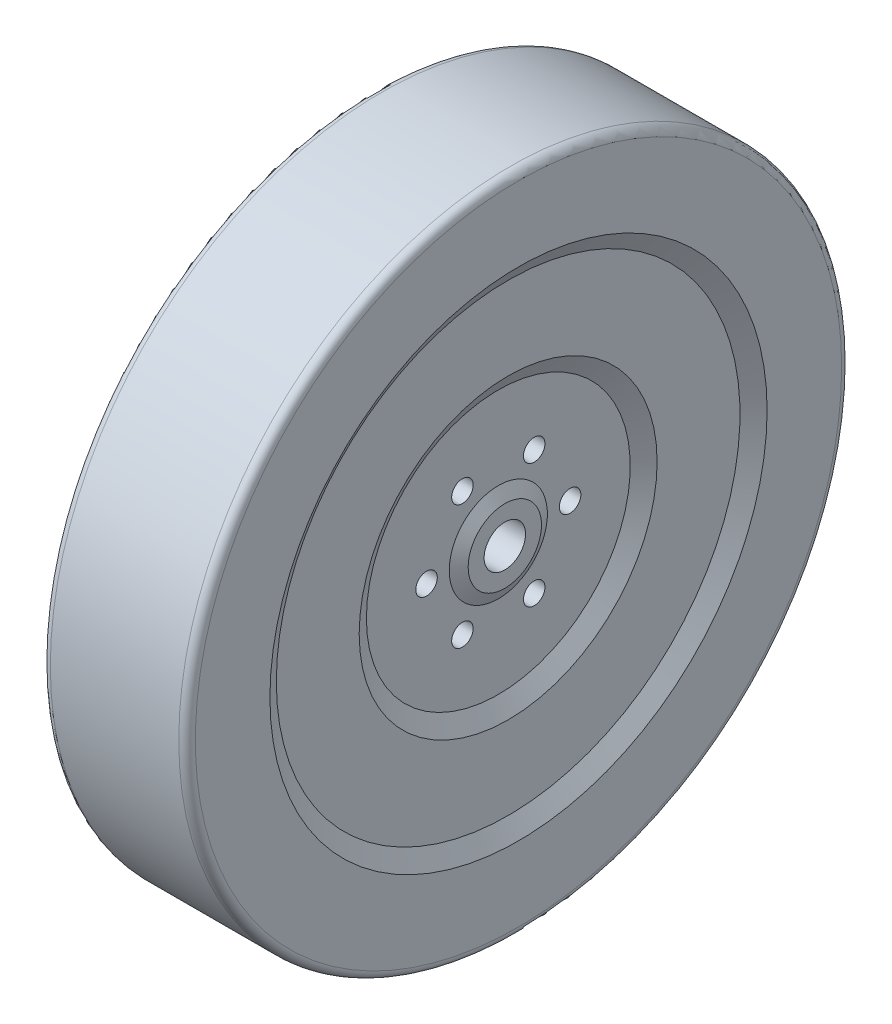
SolidWorks part; units mm, degrees
ref_plane "Front Plane" through (0, 0, 0) normal (0, 0, 1) x (1, 0, 0)
ref_plane "Top Plane" through (0, 0, 0) normal (0, 1, 0) x (1, 0, 0)
ref_plane "Right Plane" through (0, 0, 0) normal (1, 0, 0) x (0, 0, -1)
sketch "Sketch2" plane through (0, 0, 0) normal (0, 1, 0) x (1, 0, 0)
  line L1 (22.225, -101.6) -> (22.225, -76.2)
  line L2 (22.225, -76.2) -> (19.05, -71.0634)
  line L3 (19.05, -71.0634) -> (19.05, -45.6634)
  line L4 (19.05, -45.6634) -> (16.034, -40.4395)
  line L5 (16.034, -40.4395) -> (16.034, -15.0395)
  line L6 (16.034, -15.0395) -> (18.034, -11.2395)
  line L7 (18.034, -11.2395) -> (18.034, -6.35)
  line L10 (0, 0) -> (49.1946, 0) construction
  line L11 (0, 0) -> (0, -6.35) construction
  line L12 (-18.034, -6.35) -> (18.034, -6.35)
  line L13 (22.225, -101.6) -> (-22.225, -101.6)
  line L14 (0, -101.6) -> (0, -6.35) construction
  line L15 (-22.225, -101.6) -> (-22.225, -76.2)
  line L16 (-22.225, -76.2) -> (-19.05, -71.0634)
  line L17 (-19.05, -71.0634) -> (-19.05, -45.6634)
  line L18 (-19.05, -45.6634) -> (-16.034, -40.4395)
  line L19 (-16.034, -40.4395) -> (-16.034, -15.0395)
  line L20 (-16.034, -15.0395) -> (-18.034, -11.2395)
  line L21 (-18.034, -11.2395) -> (-18.034, -6.35)
  dimension "D1" = 18.034
  dimension "D2" = 22.225
  dimension "D3" = 25.4
  dimension "D4" = 25.4
  dimension "D5" = 25.4
  dimension "D6" = 4.8895
  dimension "D7" = 3.8
  dimension "D8" = 6.35
  dimension "D9" = 2
  dimension "D10" = 101.6
  dimension "D11" = 19.05
  dimension "D12" = 30
revolve "Revolve1" add sketch "Sketch2" angle 360 about L10
sketch "Sketch3" plane through (16.034, 0, 0) normal (1, 0, 0) x (0, 0, -1)
  line L0 (0, 0) -> (22, 0) construction
  line L1 (0, 0) -> (11, -19.0526) construction
  line L2 (0, 0) -> (-11, -19.0526) construction
  line L3 (0, 0) -> (-22, 0) construction
  line L4 (0, 0) -> (-11, 19.0526) construction
  line L5 (0, 0) -> (11, 19.0526) construction
  circle A0 centre (22, 0) radius 3.3
  circle A1 centre (11, -19.0526) radius 3.3
  circle A2 centre (-11, -19.0526) radius 3.3
  circle A3 centre (-22, 0) radius 3.3
  circle A4 centre (-11, 19.0526) radius 3.3
  circle A5 centre (11, 19.0526) radius 3.3
  point P17 (0, 0)
  dimension "D1" = 6.6
  dimension "D2" = 22
  dimension "D3" = 6
extrude "Cut-Extrude1" cut sketch "Sketch3" against normal through all
fillet "Fillet1" radius 2.54 2 edges at (-22.225, 0, 101.6) (22.225, 0, 101.6)
